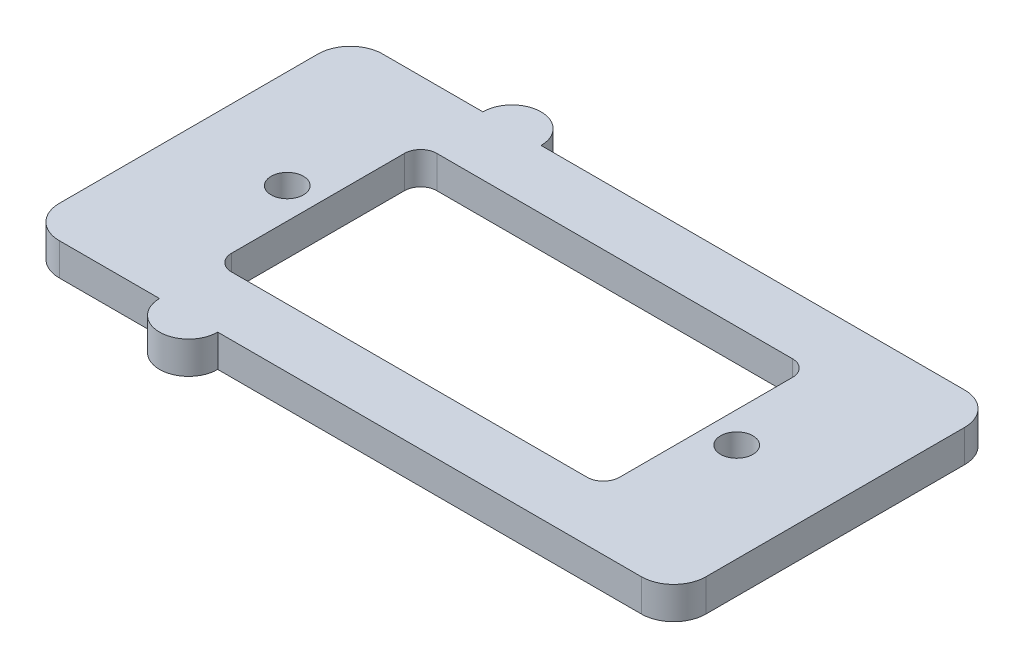
SolidWorks part; units mm, degrees
ref_plane "Plan de face" through (0, 0, 0) normal (0, 0, 1) x (1, 0, 0)
ref_plane "Plan de dessus" through (0, 0, 0) normal (0, 1, 0) x (1, 0, 0)
ref_plane "Plan de droite" through (0, 0, 0) normal (1, 0, 0) x (0, 0, -1)
sketch "Esquisse1" plane through (0, 0, 0) normal (0, 1, 0) x (1, 0, 0)
  line L0 (-13.9, 0) -> (13.9, 0) construction
  line L1 (-18, -10) -> (18, -10)
  line L2 (-20, -8) -> (-20, 8)
  line L3 (-18, 10) -> (18, 10)
  line L4 (20, -8) -> (20, 8)
  line L5 (-20, -10) -> (20, 10) construction
  line L6 (-20, 10) -> (20, -10) construction
  line L7 (-11, -6.35) -> (11, -6.35)
  line L8 (-12, -5.35) -> (-12, 5.35)
  line L9 (-11, 6.35) -> (11, 6.35)
  line L10 (12, -5.35) -> (12, 5.35)
  line L11 (-12, -6.35) -> (12, 6.35) construction
  line L12 (-12, 6.35) -> (12, -6.35) construction
  circle A0 centre (-10, 10) radius 1.8
  circle A1 centre (-10, -10) radius 1.8
  arc A2 (-11, -6.35) -> (-12, -5.35) centre (-11, -5.35) cw
  arc A4 (11, -6.35) -> (12, -5.35) centre (11, -5.35) ccw
  arc A5 (18, 10) -> (20, 8) centre (18, 8) cw
  arc A6 (11, 6.35) -> (12, 5.35) centre (11, 5.35) cw
  arc A7 (-18, -10) -> (-20, -8) centre (-18, -8) cw
  arc A8 (18, -10) -> (20, -8) centre (18, -8) ccw
  arc A9 (-20, 8) -> (-18, 10) centre (-18, 8) cw
  arc A11 (-12, 5.35) -> (-11, 6.35) centre (-11, 5.35) cw
  circle A12 centre (13.9, 0) radius 1
  circle A13 centre (-13.9, 0) radius 1
  point P0 (0, 0)
  dimension "D2" = 2
  dimension "D3" = 24
  dimension "D4" = 12.7
  dimension "D5" = 3.6
  dimension "D7" = 10
  dimension "D9" = 1
  dimension "D11" = 2
  dimension "D1" = 40
  dimension "D6" = 20
  dimension "D10" = 27.8
extrude "Boss.-Extru.1" add sketch "Esquisse1" along normal blind 2
